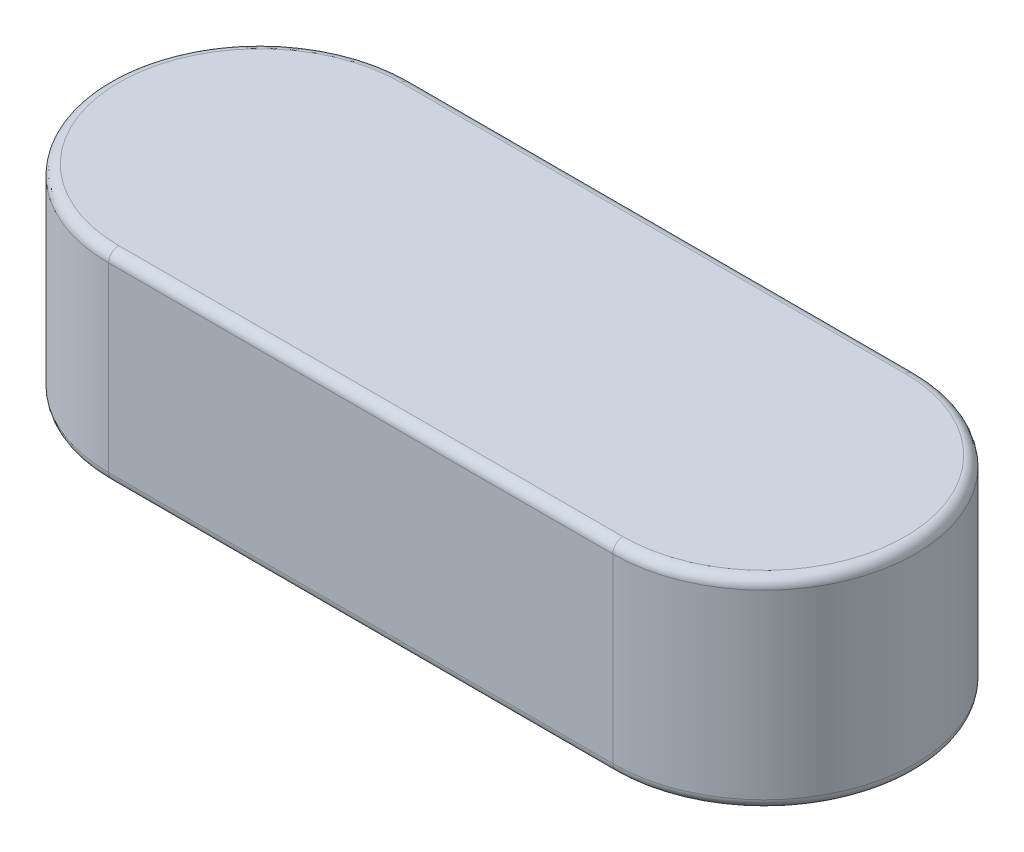
SolidWorks part; units mm, degrees
ref_plane "Front Plane" through (0, 0, 0) normal (0, 0, 1) x (1, 0, 0)
ref_plane "Top Plane" through (0, 0, 0) normal (0, 1, 0) x (1, 0, 0)
ref_plane "Right Plane" through (0, 0, 0) normal (1, 0, 0) x (0, 0, -1)
other "Configuration Table"
sketch "Sketch1" plane through (0, 0, 0) normal (0, 1, 0) x (1, 0, 0)
  line L1 (-20, 6) -> (0, 6)
  line L3 (-20, -6) -> (0, -6)
  arc A0 (0, -6) -> (0, 6) centre (0, 0) ccw
  arc A1 (-20, 6) -> (-20, -6) centre (-20, 0) ccw
  dimension "l" = 32
  dimension "b" = 12
extrude "Extrude1" add sketch "Sketch1" along normal blind 8
fillet "Fillet1" radius 0.4 8 edges at (-10, 0, -6) (6, 0, 0) (-26, 0, 0) (-10, 0, 6) (6, 8, 0) (-10, 8, 6) (-10, 8, -6) (-26, 8, 0)
